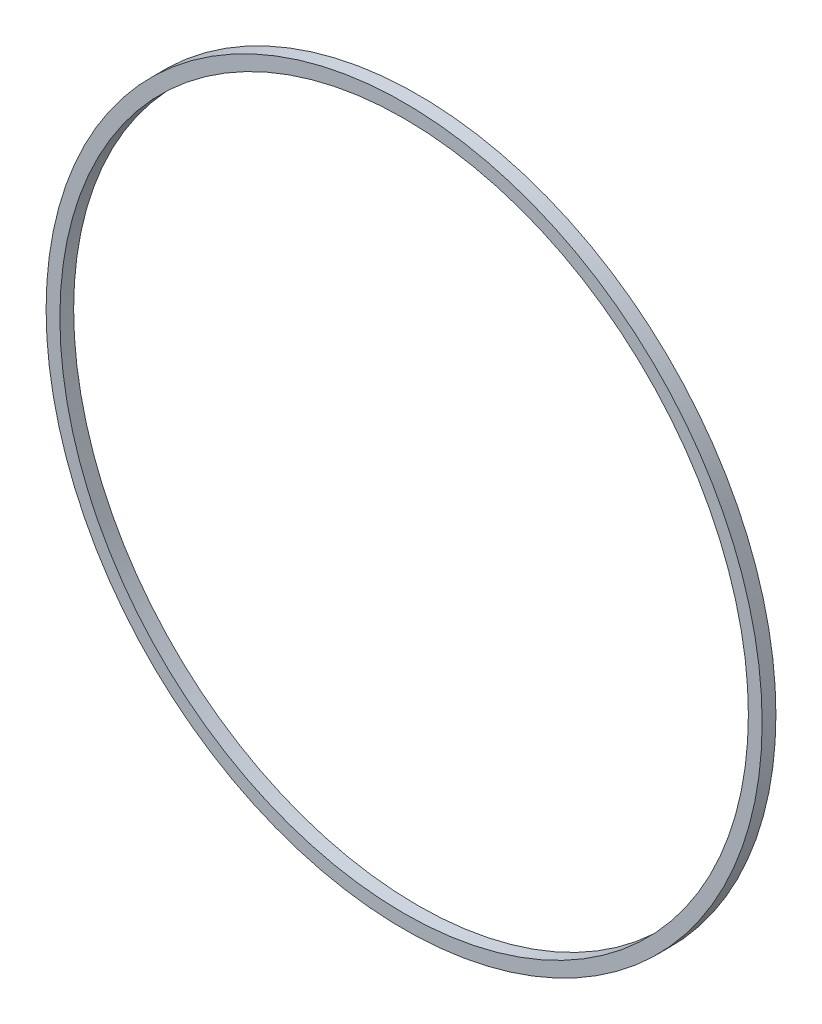
SolidWorks part; units mm, degrees
ref_plane "Front Plane" through (0, 0, 0) normal (0, 0, 1) x (1, 0, 0)
ref_plane "Top Plane" through (0, 0, 0) normal (0, 1, 0) x (1, 0, 0)
ref_plane "Right Plane" through (0, 0, 0) normal (1, 0, 0) x (0, 0, -1)
sketch "Sketch1" plane through (0, 0, 0) normal (0, 0, 1) x (1, 0, 0)
  circle A0 centre (0, 0) radius 63.5
  circle A1 centre (0, 0) radius 66.04
  dimension "D1" = 127
  dimension "D2" = 2.54
extrude "Boss-Extrude1" add sketch "Sketch1" along normal blind 2.54
